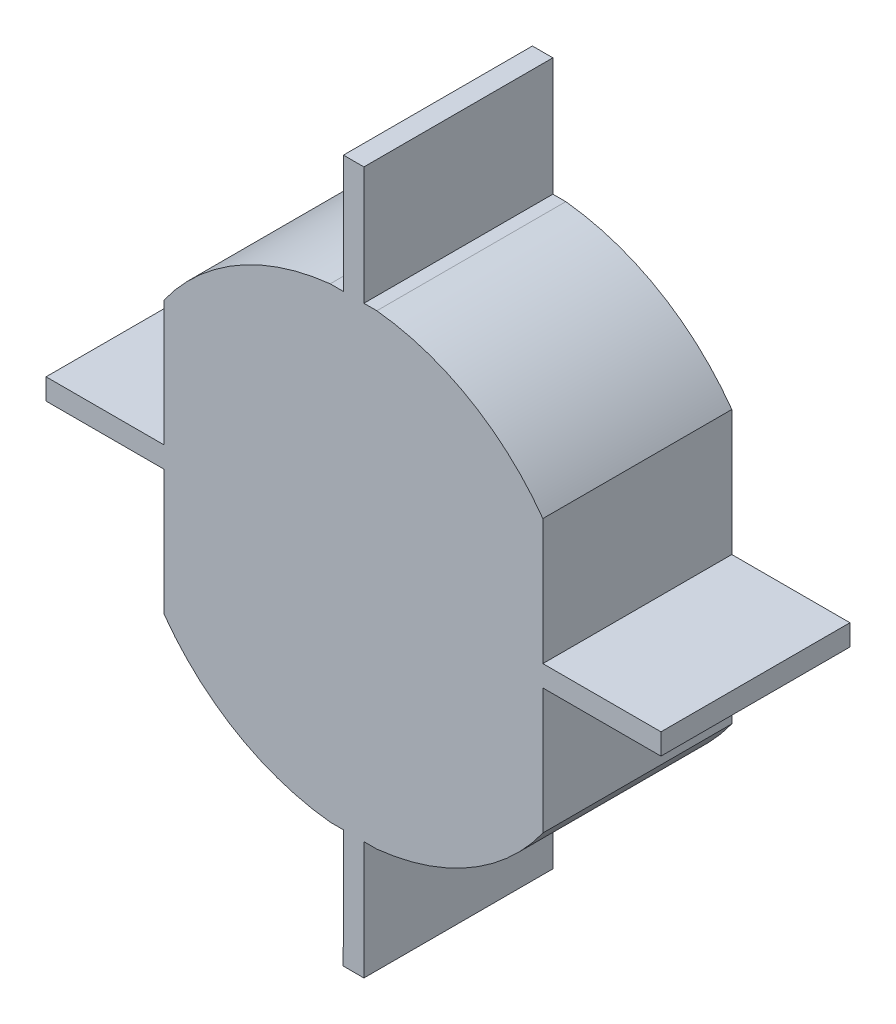
SolidWorks part; units mm, degrees
ref_plane "Front Plane" through (0, 0, 0) normal (0, 0, 1) x (1, 0, 0)
ref_plane "Top Plane" through (0, 0, 0) normal (0, 1, 0) x (1, 0, 0)
ref_plane "Right Plane" through (0, 0, 0) normal (1, 0, 0) x (0, 0, -1)
sketch "Sketch1" plane through (0, 0, 0) normal (0, 0, 1) x (1, 0, 0)
  line L0 (12.8789, 0.3) -> (12.89, 2.9988)
  line L9 (13.7562, 30.0387) -> (12.89, 30.0387)
  line L10 (12.89, 30.0387) -> (12.89, 27.3399)
  line L11 (3.3, 14.4234) -> (3.3, 8.7973)
  line L12 (12.2277, 3.3) -> (12.59, 3.3)
  line L13 (26.3332, 15.6152) -> (26.3332, 14.7234)
  line L14 (12.8789, 0.3) -> (13.7566, 0.3)
  line L15 (0.3, 15.6152) -> (0.3, 14.7234)
  line L19 (23.3328, 15.9152) -> (23.3328, 15.6152)
  line L20 (23.3328, 15.6152) -> (23.6328, 15.6152)
  line L29 (3.3, 15.9152) -> (3.3, 15.6152)
  line L30 (3.3, 15.6152) -> (3, 15.6152)
  line L36 (14.0566, 3.3) -> (13.7566, 3.3)
  line L37 (3, 14.7234) -> (3.3, 14.7234)
  line L39 (13.7562, 27.3387) -> (13.7562, 30.0387)
  line L45 (3, 15.6152) -> (0.3, 15.6152)
  line L48 (0.3, 14.7234) -> (3, 14.7234)
  line L54 (26.3332, 15.6152) -> (23.6328, 15.6152)
  line L57 (23.6332, 14.7234) -> (26.3332, 14.7234)
  line L60 (13.7566, 0.3) -> (13.7566, 3)
  line L62 (3.3, 15.9152) -> (3.3, 21.5414)
  line L64 (12.2277, 27.0387) -> (12.59, 27.0387)
  line L65 (14.0566, 3.3) -> (14.4055, 3.3)
  line L66 (23.3332, 8.7973) -> (23.3332, 14.4234)
  line L67 (23.3328, 15.9152) -> (23.3328, 21.5414)
  line L68 (14.4051, 27.0387) -> (14.0562, 27.0387)
  line L69 (13.7562, 27.3387) -> (13.7562, 27.0387)
  line L70 (13.7562, 27.0387) -> (14.0562, 27.0387)
  line L71 (12.89, 27.3399) -> (12.89, 27.0387)
  line L72 (12.89, 27.0387) -> (12.59, 27.0387)
  line L73 (23.6332, 14.7234) -> (23.3332, 14.7234)
  line L74 (23.3332, 14.7234) -> (23.3332, 14.4234)
  line L75 (13.7566, 3.3) -> (13.7566, 3)
  line L76 (3.3, 14.7234) -> (3.3, 14.4234)
  line L77 (12.89, 2.9988) -> (12.89, 3.3)
  line L78 (12.89, 3.3) -> (12.59, 3.3)
  arc A5 (3.3, 8.7973) -> (12.2277, 3.3) centre (13.3799, 15.1692) ccw
  arc A17 (12.2277, 27.0387) -> (3.3, 21.5414) centre (13.3799, 15.1695) ccw
  arc A19 (14.4055, 3.3) -> (23.3332, 8.7973) centre (13.2533, 15.1692) ccw
  arc A20 (23.3328, 21.5414) -> (14.4051, 27.0387) centre (13.2529, 15.1695) ccw
extrude "Boss-Extrude1" add sketch "Sketch1" along normal blind 8
sketch "Sketch2" plane through (0, 0, 8) normal (0, 0, 1) x (1, 0, 0)
  line L38 (12.89, 25.0387) -> (12.89, 30.0387)
  line L39 (12.89, 30.0387) -> (-3.324, 25.0765)
  line L44 (-3.324, 25.0765) -> (0.3, 15.6152)
  line L45 (0.3, 15.6152) -> (5.3, 15.6152)
  line L46 (5.3, 14.7234) -> (0.3, 14.7234)
  line L47 (0.3, 14.7234) -> (4.783, 0.075)
  line L48 (4.783, 0.075) -> (12.8789, 0.3)
  line L49 (12.8789, 0.3) -> (12.889, 5.3)
  line L50 (13.7566, 0.3) -> (13.7566, 5.3)
  line L51 (13.7566, 0.3) -> (29.0805, 10.0316)
  line L52 (29.0805, 10.0316) -> (26.3332, 14.7234)
  line L53 (26.3332, 14.7234) -> (21.3332, 14.7234)
  line L54 (21.3328, 15.6152) -> (26.3332, 15.6152)
  line L55 (26.3332, 15.6152) -> (25.6787, 25.3922)
  line L56 (25.6787, 25.3922) -> (13.7562, 30.0387)
  line L57 (13.7562, 30.0387) -> (13.7562, 25.0387)
  line L64 (5.3, 20.9332) -> (5.3, 15.6152)
  line L65 (12.89, 25.0387) -> (12.329, 25.0387)
  line L66 (5.3, 20.9332) -> (5.3, 15.6152)
  line L67 (12.89, 25.0387) -> (12.329, 25.0387)
  line L73 (21.3328, 15.6152) -> (21.3328, 20.9332)
  line L74 (14.3038, 25.0387) -> (13.7562, 25.0387)
  line L75 (21.3328, 15.6152) -> (21.3328, 20.9332)
  line L76 (14.3038, 25.0387) -> (13.7562, 25.0387)
  line L81 (13.7566, 5.3) -> (14.3042, 5.3)
  line L82 (21.3332, 9.4055) -> (21.3332, 14.7234)
  line L83 (13.7566, 5.3) -> (14.3042, 5.3)
  line L84 (21.3332, 9.4055) -> (21.3332, 14.7234)
  line L88 (5.3, 14.7234) -> (5.3, 9.4055)
  line L89 (12.329, 5.3) -> (12.89, 5.3)
  line L90 (5.3, 14.7234) -> (5.3, 9.4055)
  line L91 (12.329, 5.3) -> (12.89, 5.3)
  arc A22 (12.329, 25.0387) -> (5.3, 20.9332) centre (13.3799, 15.1695) ccw
  arc A23 (12.329, 25.0387) -> (5.3, 20.9332) centre (13.3799, 15.1695) ccw
  arc A26 (21.3328, 20.9332) -> (14.3038, 25.0387) centre (13.2529, 15.1695) ccw
  arc A27 (21.3328, 20.9332) -> (14.3038, 25.0387) centre (13.2529, 15.1695) ccw
  arc A30 (14.3042, 5.3) -> (21.3332, 9.4055) centre (13.2533, 15.1692) ccw
  arc A31 (14.3042, 5.3) -> (21.3332, 9.4055) centre (13.2533, 15.1692) ccw
  arc A35 (5.3, 9.4055) -> (12.329, 5.3) centre (13.3799, 15.1692) ccw
  arc A36 (5.3, 9.4055) -> (12.329, 5.3) centre (13.3799, 15.1692) ccw
  line M13 (12.89, 30.0387) -> (12.89, 27.0387)
  line M14 (12.89, 27.0387) -> (12.2277, 27.0387)
  arc M15 (12.2277, 27.0387) -> (3.3, 21.5414) centre (13.3799, 15.1695) ccw
  line M16 (3.3, 21.5414) -> (3.3, 15.6152)
  line M17 (3.3, 15.6152) -> (0.3, 15.6152)
  line M19 (0.3, 14.7234) -> (3.3, 14.7234)
  line M20 (3.3, 14.7234) -> (3.3, 8.7973)
  arc M21 (3.3, 8.7973) -> (12.2277, 3.3) centre (13.3799, 15.1692) ccw
  line M22 (12.2277, 3.3) -> (12.89, 3.3)
  line M26 (13.7566, 0.3) -> (13.7566, 3.3)
  line M27 (13.7566, 3.3) -> (14.4055, 3.3)
  arc M28 (14.4055, 3.3) -> (23.3332, 8.7973) centre (13.2533, 15.1692) ccw
  line M29 (23.3332, 8.7973) -> (23.3332, 14.7234)
  line M30 (23.3332, 14.7234) -> (26.3332, 14.7234)
  line M32 (26.3332, 15.6152) -> (23.3328, 15.6152)
  line M33 (23.3328, 15.6152) -> (23.3328, 21.5414)
  arc M34 (23.3328, 21.5414) -> (14.4051, 27.0387) centre (13.2529, 15.1695) ccw
  line M35 (14.4051, 27.0387) -> (13.7562, 27.0387)
  line M36 (13.7562, 27.0387) -> (13.7562, 30.0387)
  dimension "D5" = 2
  dimension "D6" = 2
  dimension "D7" = 2
  dimension "D8" = 2
extrude "Cut-Extrude2" cut sketch "Sketch2" against normal through all contours L39 L44 M17 M16 M15 M14 M13 | L55 L56 M36 M35 M34 M33 M32 | A27 L75 L54 L57 L76 M33 M34 M35 | A23 L67 L38 L45 L66 M14 M15 M16 | A36 L90 L46 L49 L91 M20 M21 M22 | L48 L49 L47 M22 M21 M20 M19 | A31 L83 L50 L53 L84 M27 M28 M29 | L51 L52 M30 M29 M28 M27 M26
